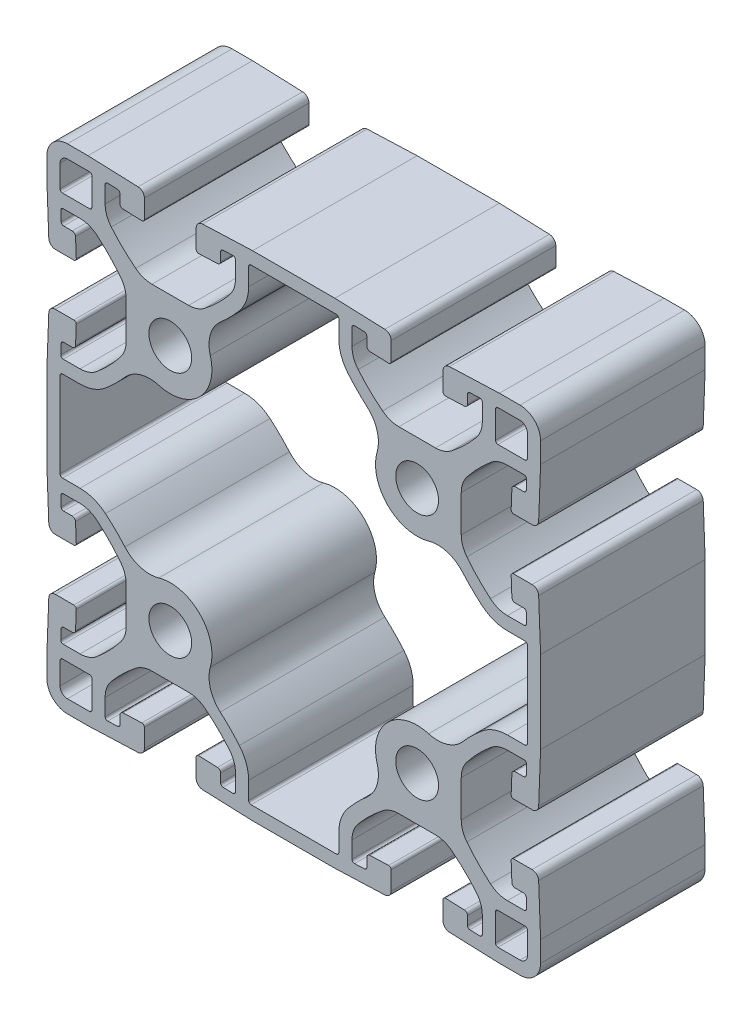
SolidWorks part; units mm, degrees
material "6061 Alloy"
ref_plane "Front" through (0, 0, 0) normal (0, 0, 1) x (1, 0, 0)
ref_plane "Top" through (0, 0, 0) normal (0, 1, 0) x (1, 0, 0)
ref_plane "Right" through (0, 0, 0) normal (1, 0, 0) x (0, 0, -1)
sketch "Sketch1" plane through (0, 0, 0) normal (0, 0, 1) x (1, 0, 0)
  line L0 (44.9072, 40.9281) -> (44.9072, 35.2719)
  line L1 (54.6191, 48.1584) -> (52.0316, 48.1584)
  line L2 (54.9998, 47.7628) -> (54.9413, 46.2388)
  line L3 (54.6191, 28.0416) -> (52.0316, 28.0416)
  line L4 (54.5606, 45.8724) -> (53.23, 45.8724)
  line L5 (54.9998, 28.4372) -> (54.9413, 29.9612)
  line L6 (52.7224, 45.3839) -> (52.6115, 42.4961)
  line L7 (54.5606, 30.3276) -> (53.23, 30.3276)
  line L8 (55.8381, 42.1005) -> (52.9922, 42.1005)
  line L9 (52.7224, 30.8161) -> (52.6115, 33.7039)
  line L10 (57.15, 50.8) -> (56.8533, 43.0775)
  line L11 (55.8381, 34.0995) -> (52.9922, 34.0995)
  line L12 (57.15, 50.8) -> (57.15, 53.975)
  line L13 (57.15, 25.4) -> (56.8533, 33.1225)
  line L14 (53.975, 57.15) -> (50.8, 57.15)
  line L15 (57.15, 19.05) -> (57.15, 25.4)
  line L16 (50.8, 57.15) -> (43.0775, 56.8533)
  line L17 (57.15, 19.05) -> (57.15, 12.7)
  line L18 (57.15, 12.7) -> (56.8533, 4.9775)
  line L19 (42.1005, 55.8381) -> (42.1005, 52.9922)
  line L20 (55.8381, 4.0005) -> (52.9922, 4.0005)
  line L21 (45.3839, 52.7224) -> (42.4961, 52.6115)
  line L22 (52.7224, 7.2839) -> (52.6115, 4.3961)
  line L23 (45.8724, 54.5606) -> (45.8724, 53.23)
  line L24 (54.5606, 7.7724) -> (53.23, 7.7724)
  line L25 (47.7628, 54.9998) -> (46.2388, 54.9413)
  line L26 (54.9998, 9.6628) -> (54.9413, 8.1388)
  line L27 (48.1584, 54.6191) -> (48.1584, 52.0316)
  line L28 (54.6191, 10.0584) -> (52.0316, 10.0584)
  line L29 (40.9281, 44.9072) -> (35.2719, 44.9072)
  line L30 (44.9072, -2.8281) -> (44.9072, 2.8281)
  line L31 (28.0416, 54.6191) -> (28.0416, 52.0316)
  line L32 (54.6191, -10.0584) -> (52.0316, -10.0584)
  line L33 (28.4372, 54.9998) -> (29.9612, 54.9413)
  line L34 (54.9998, -9.6628) -> (54.9413, -8.1388)
  line L35 (30.3276, 54.5606) -> (30.3276, 53.23)
  line L36 (54.5606, -7.7724) -> (53.23, -7.7724)
  line L37 (30.8161, 52.7224) -> (33.7039, 52.6115)
  line L38 (52.7224, -7.2839) -> (52.6115, -4.3961)
  line L39 (34.0995, 55.8381) -> (34.0995, 52.9922)
  line L40 (55.8381, -4.0005) -> (52.9922, -4.0005)
  line L41 (25.4, 57.15) -> (33.1225, 56.8533)
  line L42 (25.4, 57.15) -> (19.05, 57.15)
  line L43 (57.15, -12.7) -> (56.8533, -4.9775)
  line L44 (12.7, 57.15) -> (19.05, 57.15)
  line L45 (57.15, -12.7) -> (57.15, -15.875)
  line L46 (12.7, 57.15) -> (4.9775, 56.8533)
  line L47 (53.975, -19.05) -> (50.8, -19.05)
  line L48 (4.0005, 55.8381) -> (4.0005, 52.9922)
  line L49 (50.8, -19.05) -> (43.0775, -18.7533)
  line L50 (7.2839, 52.7224) -> (4.3961, 52.6115)
  line L51 (42.1005, -17.7381) -> (42.1005, -14.8922)
  line L52 (7.7724, 54.5606) -> (7.7724, 53.23)
  line L53 (45.3839, -14.6224) -> (42.4961, -14.5115)
  line L54 (9.6628, 54.9998) -> (8.1388, 54.9413)
  line L55 (45.8724, -16.4606) -> (45.8724, -15.13)
  line L56 (10.0584, 54.6191) -> (10.0584, 52.0316)
  line L57 (47.7628, -16.8998) -> (46.2388, -16.8413)
  line L58 (48.1584, -16.5191) -> (48.1584, -13.9316)
  line L59 (-2.8281, 44.9072) -> (2.8281, 44.9072)
  line L60 (40.9281, -6.8072) -> (35.2719, -6.8072)
  line L61 (-10.0584, 54.6191) -> (-10.0584, 52.0316)
  line L62 (-9.6628, 54.9998) -> (-8.1388, 54.9413)
  line L63 (28.0416, -16.5191) -> (28.0416, -13.9316)
  line L64 (-7.7724, 54.5606) -> (-7.7724, 53.23)
  line L65 (28.4372, -16.8998) -> (29.9612, -16.8413)
  line L66 (-7.2839, 52.7224) -> (-4.3961, 52.6115)
  line L67 (30.3276, -16.4606) -> (30.3276, -15.13)
  line L68 (-4.0005, 55.8381) -> (-4.0005, 52.9922)
  line L69 (30.8161, -14.6224) -> (33.7039, -14.5115)
  line L70 (-12.7, 57.15) -> (-4.9775, 56.8533)
  line L71 (34.0995, -17.7381) -> (34.0995, -14.8922)
  line L72 (-15.875, 57.15) -> (-12.7, 57.15)
  line L73 (25.4, -19.05) -> (33.1225, -18.7533)
  line L74 (-19.05, 50.8) -> (-19.05, 53.975)
  line L75 (25.4, -19.05) -> (19.05, -19.05)
  line L76 (-19.05, 50.8) -> (-18.7533, 43.0775)
  line L77 (12.7, -19.05) -> (19.05, -19.05)
  line L78 (12.7, -19.05) -> (4.9775, -18.7533)
  line L79 (-17.7381, 42.1005) -> (-14.8922, 42.1005)
  line L80 (4.0005, -17.7381) -> (4.0005, -14.8922)
  line L81 (-14.6224, 45.3839) -> (-14.5115, 42.4961)
  line L82 (7.2839, -14.6224) -> (4.3961, -14.5115)
  line L83 (-16.4606, 45.8724) -> (-15.13, 45.8724)
  line L84 (7.7724, -16.4606) -> (7.7724, -15.13)
  line L85 (-16.8998, 47.7628) -> (-16.8413, 46.2388)
  line L86 (9.6628, -16.8998) -> (8.1388, -16.8413)
  line L87 (-16.5191, 48.1584) -> (-13.9316, 48.1584)
  line L88 (10.0584, -16.5191) -> (10.0584, -13.9316)
  line L89 (-6.8072, 40.9281) -> (-6.8072, 35.2719)
  line L90 (-2.8281, -6.8072) -> (2.8281, -6.8072)
  line L91 (-16.5191, 28.0416) -> (-13.9316, 28.0416)
  line L92 (-10.0584, -16.5191) -> (-10.0584, -13.9316)
  line L93 (-16.8998, 28.4372) -> (-16.8413, 29.9612)
  line L94 (-9.6628, -16.8998) -> (-8.1388, -16.8413)
  line L95 (-16.4606, 30.3276) -> (-15.13, 30.3276)
  line L96 (-7.7724, -16.4606) -> (-7.7724, -15.13)
  line L97 (-14.6224, 30.8161) -> (-14.5115, 33.7039)
  line L98 (-7.2839, -14.6224) -> (-4.3961, -14.5115)
  line L99 (-17.7381, 34.0995) -> (-14.8922, 34.0995)
  line L100 (-4.0005, -17.7381) -> (-4.0005, -14.8922)
  line L101 (-19.05, 25.4) -> (-18.7533, 33.1225)
  line L102 (-19.05, 19.05) -> (-19.05, 25.4)
  line L103 (-12.7, -19.05) -> (-4.9775, -18.7533)
  line L104 (-19.05, 19.05) -> (-19.05, 12.7)
  line L105 (-15.875, -19.05) -> (-12.7, -19.05)
  line L106 (-19.05, 12.7) -> (-18.7533, 4.9775)
  line L107 (-19.05, -12.7) -> (-19.05, -15.875)
  line L108 (-17.7381, 4.0005) -> (-14.8922, 4.0005)
  line L109 (-19.05, -12.7) -> (-18.7533, -4.9775)
  line L110 (-14.6224, 7.2839) -> (-14.5115, 4.3961)
  line L111 (-17.7381, -4.0005) -> (-14.8922, -4.0005)
  line L112 (-16.4606, 7.7724) -> (-15.13, 7.7724)
  line L113 (-14.6224, -7.2839) -> (-14.5115, -4.3961)
  line L114 (-16.8998, 9.6628) -> (-16.8413, 8.1388)
  line L115 (-16.4606, -7.7724) -> (-15.13, -7.7724)
  line L116 (-16.5191, 10.0584) -> (-13.9316, 10.0584)
  line L117 (-16.8998, -9.6628) -> (-16.8413, -8.1388)
  line L118 (-16.5191, -10.0584) -> (-13.9316, -10.0584)
  line L119 (-6.8072, -2.8281) -> (-6.8072, 2.8281)
  line L120 (26.0096, 54.737) -> (26.0096, 52.0316)
  line L121 (25.6286, 55.118) -> (19.05, 55.118)
  line L122 (54.737, 26.0096) -> (52.0316, 26.0096)
  line L123 (12.4714, 55.118) -> (19.05, 55.118)
  line L124 (55.118, 19.05) -> (55.118, 25.6286)
  line L125 (12.0904, 54.737) -> (12.0904, 52.0316)
  line L126 (55.118, 19.05) -> (55.118, 12.4714)
  line L127 (54.737, 12.0904) -> (52.0316, 12.0904)
  line L128 (-16.637, 26.0096) -> (-13.9316, 26.0096)
  line L129 (-17.018, 19.05) -> (-17.018, 25.6286)
  line L130 (26.0096, -16.637) -> (26.0096, -13.9316)
  line L131 (-17.018, 19.05) -> (-17.018, 12.4714)
  line L132 (25.6286, -17.018) -> (19.05, -17.018)
  line L133 (-16.637, 12.0904) -> (-13.9316, 12.0904)
  line L134 (12.4714, -17.018) -> (19.05, -17.018)
  line L135 (12.0904, -16.637) -> (12.0904, -13.9316)
  line L136 (-17.018, -12.4714) -> (-17.018, -15.875)
  line L137 (-15.875, -17.018) -> (-12.4714, -17.018)
  line L138 (-16.637, -12.0904) -> (-12.4714, -12.0904)
  line L139 (-12.0904, -16.637) -> (-12.0904, -12.4714)
  line L140 (54.737, -12.0904) -> (50.5714, -12.0904)
  line L141 (50.1904, -16.637) -> (50.1904, -12.4714)
  line L142 (55.118, -12.4714) -> (55.118, -15.875)
  line L143 (53.975, -17.018) -> (50.5714, -17.018)
  line L144 (-12.0904, 54.737) -> (-12.0904, 50.5714)
  line L145 (-15.875, 55.118) -> (-12.4714, 55.118)
  line L146 (-16.637, 50.1904) -> (-12.4714, 50.1904)
  line L147 (-17.018, 50.5714) -> (-17.018, 53.975)
  line L148 (55.118, 50.5714) -> (55.118, 53.975)
  line L149 (53.975, 55.118) -> (50.5714, 55.118)
  line L150 (54.737, 50.1904) -> (50.5714, 50.1904)
  line L151 (50.1904, 54.737) -> (50.1904, 50.5714)
  arc A0 (45.7732, 43.4359) -> (44.9072, 40.9281) centre (48.9712, 40.9281) ccw
  arc A1 (49.4166, 47.2053) -> (45.7732, 43.4359) centre (65.7606, 27.7622) ccw
  arc A2 (52.0316, 48.1584) -> (49.4166, 47.2053) centre (52.0316, 44.0944) ccw
  arc A3 (44.9072, 35.2719) -> (45.7732, 32.7641) centre (48.9712, 35.2719) ccw
  arc A4 (45.7732, 32.7641) -> (49.4166, 28.9947) centre (65.7606, 48.4378) ccw
  arc A5 (54.9998, 47.7628) -> (54.6191, 48.1584) centre (54.6191, 47.7774) ccw
  arc A6 (49.4166, 28.9947) -> (52.0316, 28.0416) centre (52.0316, 32.1056) ccw
  arc A7 (54.5606, 45.8724) -> (54.9413, 46.2388) centre (54.5606, 46.2534) ccw
  arc A8 (54.6191, 28.0416) -> (54.9998, 28.4372) centre (54.6191, 28.4226) ccw
  arc A9 (53.23, 45.8724) -> (52.7224, 45.3839) centre (53.23, 45.3644) ccw
  arc A10 (54.9413, 29.9612) -> (54.5606, 30.3276) centre (54.5606, 29.9466) ccw
  arc A11 (52.6115, 42.4961) -> (52.9922, 42.1005) centre (52.9922, 42.4815) ccw
  arc A12 (52.7224, 30.8161) -> (53.23, 30.3276) centre (53.23, 30.8356) ccw
  arc A13 (55.8381, 42.1005) -> (56.8533, 43.0775) centre (55.8381, 43.1165) ccw
  arc A14 (52.9922, 34.0995) -> (52.6115, 33.7039) centre (52.9922, 33.7185) ccw
  arc A15 (56.8533, 33.1225) -> (55.8381, 34.0995) centre (55.8381, 33.0835) ccw
  arc A16 (57.15, 53.975) -> (53.975, 57.15) centre (53.975, 53.975) ccw
  arc A17 (43.0775, 56.8533) -> (42.1005, 55.8381) centre (43.1165, 55.8381) ccw
  arc A18 (55.8381, 4.0005) -> (56.8533, 4.9775) centre (55.8381, 5.0165) ccw
  arc A19 (42.1005, 52.9922) -> (42.4961, 52.6115) centre (42.4815, 52.9922) ccw
  arc A20 (52.6115, 4.3961) -> (52.9922, 4.0005) centre (52.9922, 4.3815) ccw
  arc A21 (45.3839, 52.7224) -> (45.8724, 53.23) centre (45.3644, 53.23) ccw
  arc A22 (53.23, 7.7724) -> (52.7224, 7.2839) centre (53.23, 7.2644) ccw
  arc A23 (46.2388, 54.9413) -> (45.8724, 54.5606) centre (46.2534, 54.5606) ccw
  arc A24 (54.5606, 7.7724) -> (54.9413, 8.1388) centre (54.5606, 8.1534) ccw
  arc A25 (48.1584, 54.6191) -> (47.7628, 54.9998) centre (47.7774, 54.6191) ccw
  arc A26 (54.9998, 9.6628) -> (54.6191, 10.0584) centre (54.6191, 9.6774) ccw
  arc A27 (47.2053, 49.4166) -> (48.1584, 52.0316) centre (44.0944, 52.0316) ccw
  arc A28 (43.4359, 45.7732) -> (47.2053, 49.4166) centre (27.7622, 65.7606) ccw
  arc A29 (52.0316, 10.0584) -> (49.4166, 9.1053) centre (52.0316, 5.9944) ccw
  arc A30 (40.9281, 44.9072) -> (43.4359, 45.7732) centre (40.9281, 48.9712) ccw
  arc A31 (49.4166, 9.1053) -> (45.7732, 5.3359) centre (65.7606, -10.3378) ccw
  arc A32 (45.7732, 5.3359) -> (44.9072, 2.8281) centre (48.9712, 2.8281) ccw
  arc A33 (32.7641, 45.7732) -> (35.2719, 44.9072) centre (35.2719, 48.9712) ccw
  arc A34 (28.9947, 49.4166) -> (32.7641, 45.7732) centre (48.4378, 65.7606) ccw
  arc A35 (44.9072, -2.8281) -> (45.7732, -5.3359) centre (48.9712, -2.8281) ccw
  arc A36 (28.0416, 52.0316) -> (28.9947, 49.4166) centre (32.1056, 52.0316) ccw
  arc A37 (45.7732, -5.3359) -> (49.4166, -9.1053) centre (65.7606, 10.3378) ccw
  arc A38 (49.4166, -9.1053) -> (52.0316, -10.0584) centre (52.0316, -5.9944) ccw
  arc A39 (28.4372, 54.9998) -> (28.0416, 54.6191) centre (28.4226, 54.6191) ccw
  arc A40 (54.6191, -10.0584) -> (54.9998, -9.6628) centre (54.6191, -9.6774) ccw
  arc A41 (30.3276, 54.5606) -> (29.9612, 54.9413) centre (29.9466, 54.5606) ccw
  arc A42 (54.9413, -8.1388) -> (54.5606, -7.7724) centre (54.5606, -8.1534) ccw
  arc A43 (30.3276, 53.23) -> (30.8161, 52.7224) centre (30.8356, 53.23) ccw
  arc A44 (52.7224, -7.2839) -> (53.23, -7.7724) centre (53.23, -7.2644) ccw
  arc A45 (33.7039, 52.6115) -> (34.0995, 52.9922) centre (33.7185, 52.9922) ccw
  arc A46 (52.9922, -4.0005) -> (52.6115, -4.3961) centre (52.9922, -4.3815) ccw
  arc A47 (34.0995, 55.8381) -> (33.1225, 56.8533) centre (33.0835, 55.8381) ccw
  arc A48 (56.8533, -4.9775) -> (55.8381, -4.0005) centre (55.8381, -5.0165) ccw
  arc A49 (53.975, -19.05) -> (57.15, -15.875) centre (53.975, -15.875) ccw
  arc A50 (4.9775, 56.8533) -> (4.0005, 55.8381) centre (5.0165, 55.8381) ccw
  arc A51 (4.0005, 52.9922) -> (4.3961, 52.6115) centre (4.3815, 52.9922) ccw
  arc A52 (42.1005, -17.7381) -> (43.0775, -18.7533) centre (43.1165, -17.7381) ccw
  arc A53 (7.2839, 52.7224) -> (7.7724, 53.23) centre (7.2644, 53.23) ccw
  arc A54 (42.4961, -14.5115) -> (42.1005, -14.8922) centre (42.4815, -14.8922) ccw
  arc A55 (8.1388, 54.9413) -> (7.7724, 54.5606) centre (8.1534, 54.5606) ccw
  arc A56 (45.8724, -15.13) -> (45.3839, -14.6224) centre (45.3644, -15.13) ccw
  arc A57 (10.0584, 54.6191) -> (9.6628, 54.9998) centre (9.6774, 54.6191) ccw
  arc A58 (45.8724, -16.4606) -> (46.2388, -16.8413) centre (46.2534, -16.4606) ccw
  arc A59 (9.1053, 49.4166) -> (10.0584, 52.0316) centre (5.9944, 52.0316) ccw
  arc A60 (47.7628, -16.8998) -> (48.1584, -16.5191) centre (47.7774, -16.5191) ccw
  arc A61 (5.3359, 45.7732) -> (9.1053, 49.4166) centre (-10.3378, 65.7606) ccw
  arc A62 (2.8281, 44.9072) -> (5.3359, 45.7732) centre (2.8281, 48.9712) ccw
  arc A63 (48.1584, -13.9316) -> (47.2053, -11.3166) centre (44.0944, -13.9316) ccw
  arc A64 (47.2053, -11.3166) -> (43.4359, -7.6732) centre (27.7622, -27.6606) ccw
  arc A65 (-5.3359, 45.7732) -> (-2.8281, 44.9072) centre (-2.8281, 48.9712) ccw
  arc A66 (43.4359, -7.6732) -> (40.9281, -6.8072) centre (40.9281, -10.8712) ccw
  arc A67 (-9.1053, 49.4166) -> (-5.3359, 45.7732) centre (10.3378, 65.7606) ccw
  arc A68 (-10.0584, 52.0316) -> (-9.1053, 49.4166) centre (-5.9944, 52.0316) ccw
  arc A69 (35.2719, -6.8072) -> (32.7641, -7.6732) centre (35.2719, -10.8712) ccw
  arc A70 (32.7641, -7.6732) -> (28.9947, -11.3166) centre (48.4378, -27.6606) ccw
  arc A71 (-9.6628, 54.9998) -> (-10.0584, 54.6191) centre (-9.6774, 54.6191) ccw
  arc A72 (28.9947, -11.3166) -> (28.0416, -13.9316) centre (32.1056, -13.9316) ccw
  arc A73 (-7.7724, 54.5606) -> (-8.1388, 54.9413) centre (-8.1534, 54.5606) ccw
  arc A74 (28.0416, -16.5191) -> (28.4372, -16.8998) centre (28.4226, -16.5191) ccw
  arc A75 (-7.7724, 53.23) -> (-7.2839, 52.7224) centre (-7.2644, 53.23) ccw
  arc A76 (29.9612, -16.8413) -> (30.3276, -16.4606) centre (29.9466, -16.4606) ccw
  arc A77 (-4.3961, 52.6115) -> (-4.0005, 52.9922) centre (-4.3815, 52.9922) ccw
  arc A78 (30.8161, -14.6224) -> (30.3276, -15.13) centre (30.8356, -15.13) ccw
  arc A79 (-4.0005, 55.8381) -> (-4.9775, 56.8533) centre (-5.0165, 55.8381) ccw
  arc A80 (34.0995, -14.8922) -> (33.7039, -14.5115) centre (33.7185, -14.8922) ccw
  arc A81 (33.1225, -18.7533) -> (34.0995, -17.7381) centre (33.0835, -17.7381) ccw
  arc A82 (-15.875, 57.15) -> (-19.05, 53.975) centre (-15.875, 53.975) ccw
  arc A83 (-18.7533, 43.0775) -> (-17.7381, 42.1005) centre (-17.7381, 43.1165) ccw
  arc A84 (4.0005, -17.7381) -> (4.9775, -18.7533) centre (5.0165, -17.7381) ccw
  arc A85 (-14.8922, 42.1005) -> (-14.5115, 42.4961) centre (-14.8922, 42.4815) ccw
  arc A86 (4.3961, -14.5115) -> (4.0005, -14.8922) centre (4.3815, -14.8922) ccw
  arc A87 (-14.6224, 45.3839) -> (-15.13, 45.8724) centre (-15.13, 45.3644) ccw
  arc A88 (7.7724, -15.13) -> (7.2839, -14.6224) centre (7.2644, -15.13) ccw
  arc A89 (-16.8413, 46.2388) -> (-16.4606, 45.8724) centre (-16.4606, 46.2534) ccw
  arc A90 (7.7724, -16.4606) -> (8.1388, -16.8413) centre (8.1534, -16.4606) ccw
  arc A91 (-16.5191, 48.1584) -> (-16.8998, 47.7628) centre (-16.5191, 47.7774) ccw
  arc A92 (9.6628, -16.8998) -> (10.0584, -16.5191) centre (9.6774, -16.5191) ccw
  arc A93 (-11.3166, 47.2053) -> (-13.9316, 48.1584) centre (-13.9316, 44.0944) ccw
  arc A94 (-7.6732, 43.4359) -> (-11.3166, 47.2053) centre (-27.6606, 27.7622) ccw
  arc A95 (10.0584, -13.9316) -> (9.1053, -11.3166) centre (5.9944, -13.9316) ccw
  arc A96 (-6.8072, 40.9281) -> (-7.6732, 43.4359) centre (-10.8712, 40.9281) ccw
  arc A97 (9.1053, -11.3166) -> (5.3359, -7.6732) centre (-10.3378, -27.6606) ccw
  arc A98 (5.3359, -7.6732) -> (2.8281, -6.8072) centre (2.8281, -10.8712) ccw
  arc A99 (-7.6732, 32.7641) -> (-6.8072, 35.2719) centre (-10.8712, 35.2719) ccw
  arc A100 (-11.3166, 28.9947) -> (-7.6732, 32.7641) centre (-27.6606, 48.4378) ccw
  arc A101 (-2.8281, -6.8072) -> (-5.3359, -7.6732) centre (-2.8281, -10.8712) ccw
  arc A102 (-13.9316, 28.0416) -> (-11.3166, 28.9947) centre (-13.9316, 32.1056) ccw
  arc A103 (-5.3359, -7.6732) -> (-9.1053, -11.3166) centre (10.3378, -27.6606) ccw
  arc A104 (-9.1053, -11.3166) -> (-10.0584, -13.9316) centre (-5.9944, -13.9316) ccw
  arc A105 (-16.8998, 28.4372) -> (-16.5191, 28.0416) centre (-16.5191, 28.4226) ccw
  arc A106 (-10.0584, -16.5191) -> (-9.6628, -16.8998) centre (-9.6774, -16.5191) ccw
  arc A107 (-16.4606, 30.3276) -> (-16.8413, 29.9612) centre (-16.4606, 29.9466) ccw
  arc A108 (-8.1388, -16.8413) -> (-7.7724, -16.4606) centre (-8.1534, -16.4606) ccw
  arc A109 (-15.13, 30.3276) -> (-14.6224, 30.8161) centre (-15.13, 30.8356) ccw
  arc A110 (-7.2839, -14.6224) -> (-7.7724, -15.13) centre (-7.2644, -15.13) ccw
  arc A111 (-14.5115, 33.7039) -> (-14.8922, 34.0995) centre (-14.8922, 33.7185) ccw
  arc A112 (-4.0005, -14.8922) -> (-4.3961, -14.5115) centre (-4.3815, -14.8922) ccw
  arc A113 (-17.7381, 34.0995) -> (-18.7533, 33.1225) centre (-17.7381, 33.0835) ccw
  arc A114 (-4.9775, -18.7533) -> (-4.0005, -17.7381) centre (-5.0165, -17.7381) ccw
  arc A115 (-19.05, -15.875) -> (-15.875, -19.05) centre (-15.875, -15.875) ccw
  arc A116 (-18.7533, 4.9775) -> (-17.7381, 4.0005) centre (-17.7381, 5.0165) ccw
  arc A117 (-14.8922, 4.0005) -> (-14.5115, 4.3961) centre (-14.8922, 4.3815) ccw
  arc A118 (-17.7381, -4.0005) -> (-18.7533, -4.9775) centre (-17.7381, -5.0165) ccw
  arc A119 (-14.6224, 7.2839) -> (-15.13, 7.7724) centre (-15.13, 7.2644) ccw
  arc A120 (-14.5115, -4.3961) -> (-14.8922, -4.0005) centre (-14.8922, -4.3815) ccw
  arc A121 (-16.8413, 8.1388) -> (-16.4606, 7.7724) centre (-16.4606, 8.1534) ccw
  arc A122 (-15.13, -7.7724) -> (-14.6224, -7.2839) centre (-15.13, -7.2644) ccw
  arc A123 (-16.5191, 10.0584) -> (-16.8998, 9.6628) centre (-16.5191, 9.6774) ccw
  arc A124 (-16.4606, -7.7724) -> (-16.8413, -8.1388) centre (-16.4606, -8.1534) ccw
  arc A125 (-11.3166, 9.1053) -> (-13.9316, 10.0584) centre (-13.9316, 5.9944) ccw
  arc A126 (-16.8998, -9.6628) -> (-16.5191, -10.0584) centre (-16.5191, -9.6774) ccw
  arc A127 (-7.6732, 5.3359) -> (-11.3166, 9.1053) centre (-27.6606, -10.3378) ccw
  arc A128 (-6.8072, 2.8281) -> (-7.6732, 5.3359) centre (-10.8712, 2.8281) ccw
  arc A129 (-13.9316, -10.0584) -> (-11.3166, -9.1053) centre (-13.9316, -5.9944) ccw
  arc A130 (-11.3166, -9.1053) -> (-7.6732, -5.3359) centre (-27.6606, 10.3378) ccw
  arc A131 (-7.6732, -5.3359) -> (-6.8072, -2.8281) centre (-10.8712, -2.8281) ccw
  arc A132 (31.9242, 39.8765) -> (30.3853, 45.1058) centre (27.0422, 41.2808) ccw
  arc A133 (27.4393, 48.1091) -> (30.3853, 45.1058) centre (48.4378, 65.7606) ccw
  arc A134 (31.9242, 39.8765) -> (39.8765, 31.9242) centre (38.1, 38.1) ccw
  arc A135 (26.0096, 52.0316) -> (27.4393, 48.1091) centre (32.1056, 52.0316) ccw
  arc A136 (45.1058, 30.3853) -> (39.8765, 31.9242) centre (41.2808, 27.0422) ccw
  arc A137 (45.1058, 30.3853) -> (48.1091, 27.4393) centre (65.7606, 48.4378) ccw
  arc A138 (26.0096, 54.737) -> (25.6286, 55.118) centre (25.6286, 54.737) ccw
  arc A139 (48.1091, 27.4393) -> (52.0316, 26.0096) centre (52.0316, 32.1056) ccw
  arc A140 (55.118, 25.6286) -> (54.737, 26.0096) centre (54.737, 25.6286) ccw
  arc A141 (12.4714, 55.118) -> (12.0904, 54.737) centre (12.4714, 54.737) ccw
  arc A142 (10.6607, 48.1091) -> (12.0904, 52.0316) centre (5.9944, 52.0316) ccw
  arc A143 (54.737, 12.0904) -> (55.118, 12.4714) centre (54.737, 12.4714) ccw
  arc A144 (7.7147, 45.1058) -> (10.6607, 48.1091) centre (-10.3378, 65.7606) ccw
  arc A145 (7.7147, 45.1058) -> (6.1758, 39.8765) centre (11.0578, 41.2808) ccw
  arc A146 (52.0316, 12.0904) -> (48.1091, 10.6607) centre (52.0316, 5.9944) ccw
  arc A147 (-1.7765, 31.9242) -> (6.1758, 39.8765) centre (0, 38.1) ccw
  arc A148 (48.1091, 10.6607) -> (45.1058, 7.7147) centre (65.7606, -10.3378) ccw
  arc A149 (-1.7765, 31.9242) -> (-7.0058, 30.3853) centre (-3.1808, 27.0422) ccw
  arc A150 (39.8765, 6.1758) -> (45.1058, 7.7147) centre (41.2808, 11.0578) ccw
  arc A151 (-10.0091, 27.4393) -> (-7.0058, 30.3853) centre (-27.6606, 48.4378) ccw
  arc A152 (39.8765, 6.1758) -> (31.9242, -1.7765) centre (38.1, 0) ccw
  arc A153 (-13.9316, 26.0096) -> (-10.0091, 27.4393) centre (-13.9316, 32.1056) ccw
  arc A154 (30.3853, -7.0058) -> (31.9242, -1.7765) centre (27.0422, -3.1808) ccw
  arc A155 (30.3853, -7.0058) -> (27.4393, -10.0091) centre (48.4378, -27.6606) ccw
  arc A156 (-16.637, 26.0096) -> (-17.018, 25.6286) centre (-16.637, 25.6286) ccw
  arc A157 (27.4393, -10.0091) -> (26.0096, -13.9316) centre (32.1056, -13.9316) ccw
  arc A158 (25.6286, -17.018) -> (26.0096, -16.637) centre (25.6286, -16.637) ccw
  arc A159 (-17.018, 12.4714) -> (-16.637, 12.0904) centre (-16.637, 12.4714) ccw
  arc A160 (-10.0091, 10.6607) -> (-13.9316, 12.0904) centre (-13.9316, 5.9944) ccw
  arc A161 (12.0904, -16.637) -> (12.4714, -17.018) centre (12.4714, -16.637) ccw
  arc A162 (-7.0058, 7.7147) -> (-10.0091, 10.6607) centre (-27.6606, -10.3378) ccw
  arc A163 (-7.0058, 7.7147) -> (-1.7765, 6.1758) centre (-3.1808, 11.0578) ccw
  arc A164 (12.0904, -13.9316) -> (10.6607, -10.0091) centre (5.9944, -13.9316) ccw
  arc A165 (6.1758, -1.7765) -> (-1.7765, 6.1758) centre (0, 0) ccw
  arc A166 (10.6607, -10.0091) -> (7.7147, -7.0058) centre (-10.3378, -27.6606) ccw
  arc A167 (6.1758, -1.7765) -> (7.7147, -7.0058) centre (11.0578, -3.1808) ccw
  arc A168 (-17.018, -15.875) -> (-15.875, -17.018) centre (-15.875, -15.875) ccw
  arc A169 (-16.637, -12.0904) -> (-17.018, -12.4714) centre (-16.637, -12.4714) ccw
  arc A170 (-12.4714, -17.018) -> (-12.0904, -16.637) centre (-12.4714, -16.637) ccw
  arc A171 (-12.0904, -12.4714) -> (-12.4714, -12.0904) centre (-12.4714, -12.4714) ccw
  circle A172 centre (0, 0) radius 3.302
  circle A173 centre (0, 38.1) radius 3.302
  arc A174 (50.5714, -12.0904) -> (50.1904, -12.4714) centre (50.5714, -12.4714) ccw
  arc A175 (55.118, -12.4714) -> (54.737, -12.0904) centre (54.737, -12.4714) ccw
  arc A176 (50.1904, -16.637) -> (50.5714, -17.018) centre (50.5714, -16.637) ccw
  arc A177 (53.975, -17.018) -> (55.118, -15.875) centre (53.975, -15.875) ccw
  circle A178 centre (38.1, 0) radius 3.302
  circle A179 centre (38.1, 38.1) radius 3.302
  arc A180 (-12.0904, 54.737) -> (-12.4714, 55.118) centre (-12.4714, 54.737) ccw
  arc A181 (-12.4714, 50.1904) -> (-12.0904, 50.5714) centre (-12.4714, 50.5714) ccw
  arc A182 (-15.875, 55.118) -> (-17.018, 53.975) centre (-15.875, 53.975) ccw
  arc A183 (-17.018, 50.5714) -> (-16.637, 50.1904) centre (-16.637, 50.5714) ccw
  arc A184 (55.118, 53.975) -> (53.975, 55.118) centre (53.975, 53.975) ccw
  arc A185 (54.737, 50.1904) -> (55.118, 50.5714) centre (54.737, 50.5714) ccw
  arc A186 (50.5714, 55.118) -> (50.1904, 54.737) centre (50.5714, 54.737) ccw
  arc A187 (50.1904, 50.5714) -> (50.5714, 50.1904) centre (50.5714, 50.5714) ccw
extrude "Extrude1" add sketch "Sketch1" along normal blind 25.4
